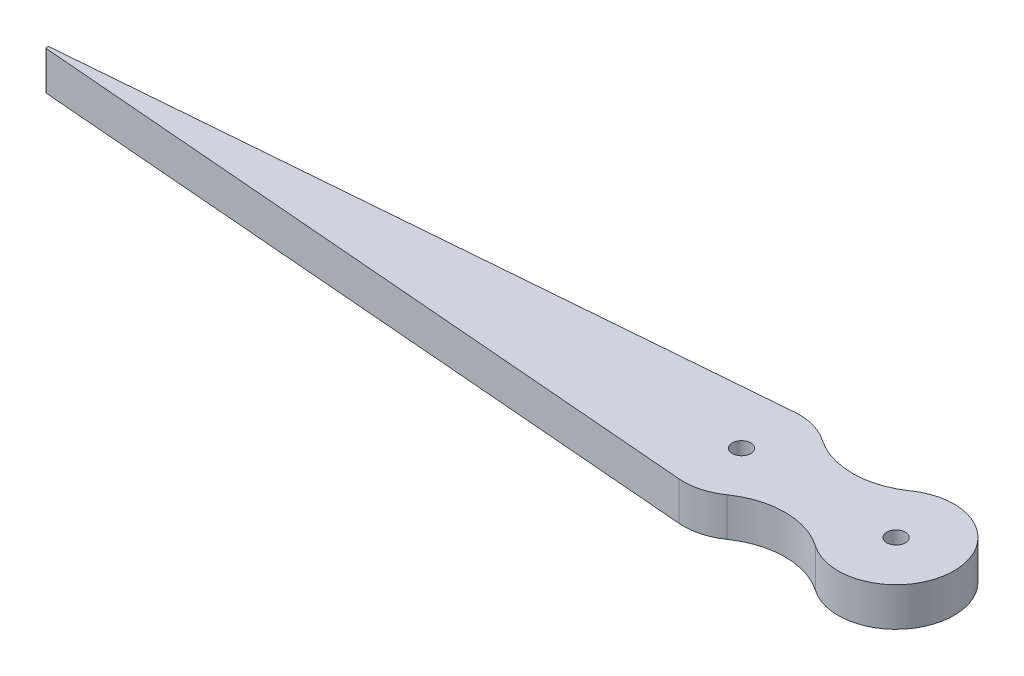
SolidWorks part; units mm, degrees
material "Alum Plate"
ref_plane "Front Plane" through (0, 0, 0) normal (0, 0, 1) x (1, 0, 0)
ref_plane "Top Plane" through (0, 0, 0) normal (0, 1, 0) x (1, 0, 0)
ref_plane "Right Plane" through (0, 0, 0) normal (1, 0, 0) x (0, 0, -1)
other "Bounding Box"
ref_plane "Default Plane" through (13.8565, 3.175, 6.7999) normal (0, -1, 0) x (-1, 0, 0)
sketch "Sketch1" plane through (0, 0, 0) normal (0, 1, 0) x (1, 0, 0)
  line L0 (0, 0) -> (25.4, 0) construction
  line L1 (0, 0) -> (-7.741, 7.741) construction
  line L2 (-7.741, 7.741) -> (-67.9351, -52.4531) construction
  line L3 (-0.7749, 9.4934) -> (-117.082, 0)
  line L4 (-117.082, 0) -> (-0.7749, -9.4934)
  line L5 (-117.082, 0) -> (-15.482, 0) construction
  circle A0 centre (0, 0) radius 1.524
  arc A1 (5.4429, 7.8167) -> (-0.7749, 9.4934) centre (0, 0) ccw
  circle A2 centre (25.4, 0) radius 1.524
  arc A3 (19.9571, -7.8167) -> (19.9571, 7.8167) centre (25.4, 0) ccw
  arc A4 (5.4429, 7.8167) -> (19.9571, 7.8167) centre (12.7, 18.239) ccw
  arc A5 (19.9571, -7.8167) -> (5.4429, -7.8167) centre (12.7, -18.239) ccw
  arc A6 (-0.7749, -9.4934) -> (5.4429, -7.8167) centre (0, 0) ccw
  dimension "D4" = 3.048
  dimension "D5" = 19.05
  dimension "D6" = 25.4
  dimension "D1" = 45
  dimension "D2" = 10.9474
  dimension "D3" = 25.4
  dimension "D7" = 101.6
extrude "Boss-Extrude1" add sketch "Sketch1" along normal blind 6.35
fillet "Fillet1" radius 0.254 1 edges at (-117.082, 3.175, 0)
